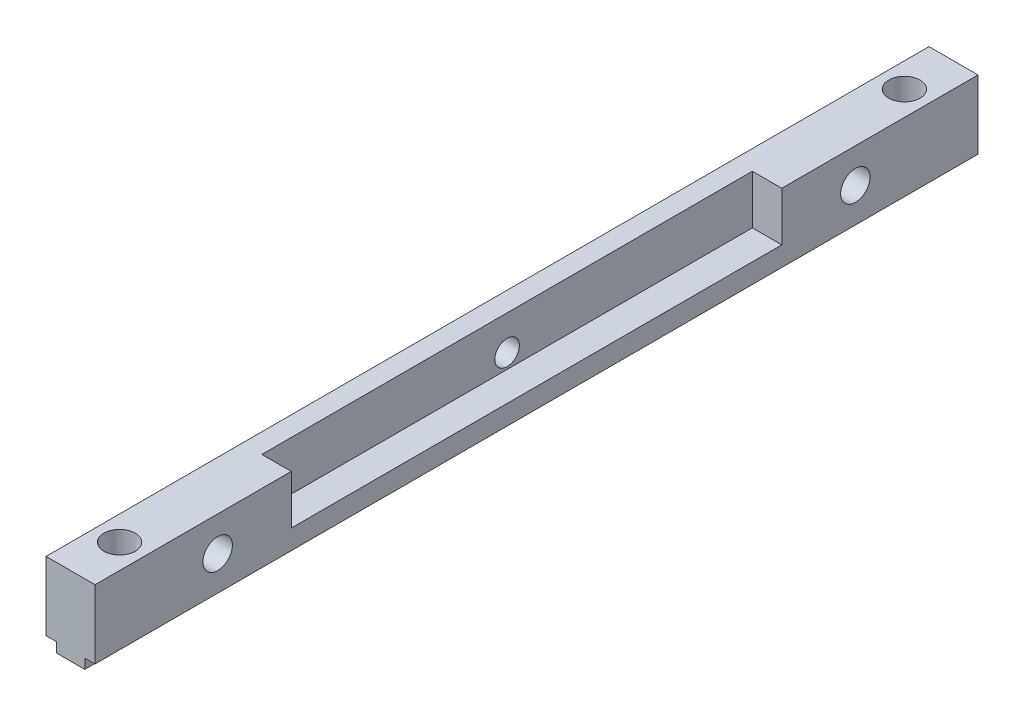
SolidWorks part; units mm, degrees
ref_plane "Front Plane" through (0, 0, 0) normal (0, 0, 1) x (1, 0, 0)
ref_plane "Top Plane" through (0, 0, 0) normal (0, 1, 0) x (1, 0, 0)
ref_plane "Right Plane" through (0, 0, 0) normal (1, 0, 0) x (0, 0, -1)
sketch "Esquisse1" plane through (0, 0, 0) normal (0, 0, 1) x (1, 0, 0)
  line L0 (0, 7) -> (5, 7)
  line L1 (5, 7) -> (5, 0)
  line L2 (5, 0) -> (3.95, 0)
  line L3 (3.95, 0) -> (3.95, -1)
  line L4 (3.95, -1) -> (1.05, -1)
  line L5 (1.05, -1) -> (1.05, 0)
  line L6 (1.05, 0) -> (0, 0)
  line L7 (0, 0) -> (0, 7)
  dimension "D1" = 1.05
  dimension "D2" = 7
  dimension "D3" = 1
  dimension "D4" = 2.9
  dimension "D5" = 1.05
  dimension "D6" = 5
extrude "Main" add sketch "Esquisse1" along normal blind 90
sketch "Esquisse2" plane through (5, 0, 0) normal (1, 0, 0) x (0, 0, -1)
  line L1 (-77.5, 3.5) -> (-12.5, 3.5) construction
  line L2 (-90, 0) -> (0, 0) construction
  line L3 (-90, 7) -> (0, 7) construction
  circle A0 centre (-12.5, 3.5) radius 1.5
  circle A1 centre (-77.5, 3.5) radius 1.5
  point P4 (-45, 7.5)
  point P8 (-45, 7)
  point P9 (-45, 3.5)
  point P10 (0, 0)
  point P13 (-45, 10)
  point P14 (0, 0)
  dimension "D1" = 65
  dimension "D4" = 3
  dimension "D3" = 3.5
extrude "HolesForPowerBoard" cut sketch "Esquisse2" against normal through all
sketch "Esquisse4" plane through (0, -1, 0) normal (0, -1, 0) x (-1, 0, 0)
  line L0 (0, -90) -> (0, 0) construction
  line L1 (-1.05, -90) -> (-3.95, -90) construction
  line L2 (-1.05, 0) -> (-3.95, 0) construction
  circle A0 centre (-2.5, -85) radius 1.6
  circle A1 centre (-2.5, -5) radius 1.6
  dimension "D1" = 3.2
  dimension "D2" = 2.5
  dimension "D3" = 5
  dimension "D4" = 5
extrude "HolesForMakerBeam" cut sketch "Esquisse4" against normal through all
sketch "Sketch1" plane through (5, 0, 0) normal (1, 0, 0) x (0, 0, -1)
  line L0 (-90, 7) -> (0, 7) construction
  line L1 (-20, 2) -> (-70, 2)
  line L2 (-20, 2) -> (-20, 7)
  line L3 (-20, 7) -> (-70, 7)
  line L4 (-70, 2) -> (-70, 7)
  line L5 (0, 0) -> (0, 7) construction
  line L6 (-90, 0) -> (-90, 7) construction
  point P8 (0, 3.5)
  dimension "D1" = 20
  dimension "D2" = 20
  dimension "D3" = 5
extrude "PowerBoardPinHoles" cut sketch "Sketch1" against normal blind 3
sketch "Sketch2" plane through (0, 0, 0) normal (-1, 0, 0) x (0, 0, 1)
  line L0 (90, 7) -> (0, 7) construction
  circle A0 centre (45, 3.5) radius 1.25
  point P2 (0, 0)
  point P3 (45, 7)
  dimension "D1" = 2.5
  dimension "D2" = 3.5
extrude "WindowFixHoles" cut sketch "Sketch2" against normal through all
